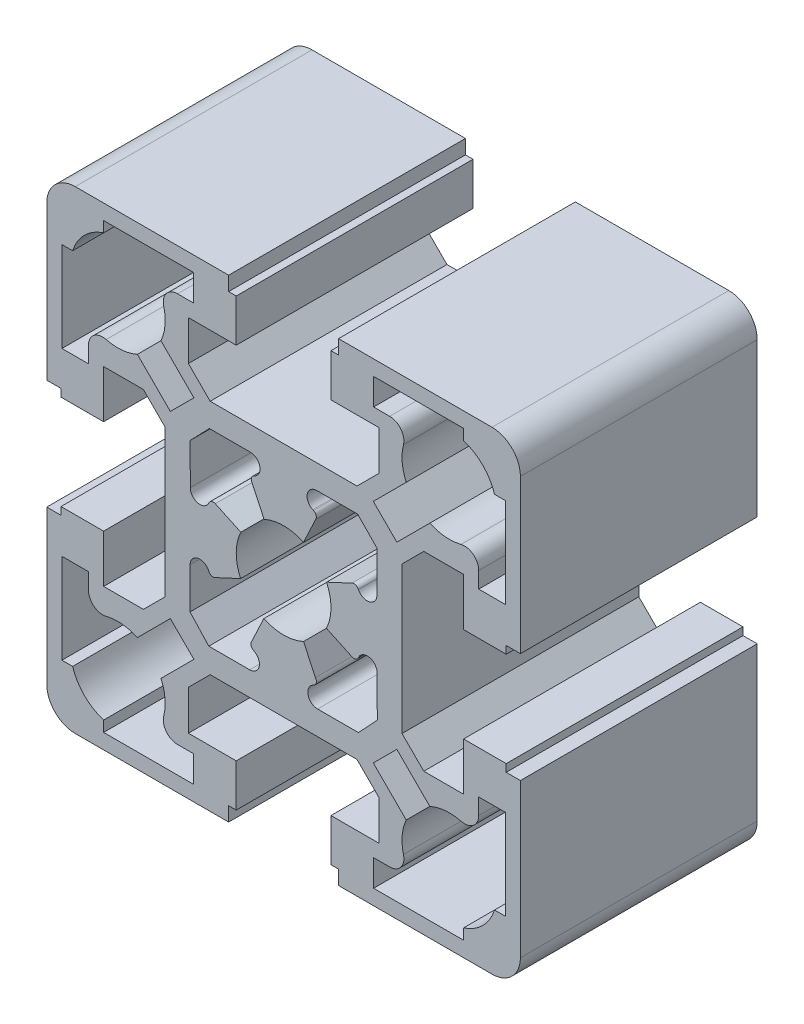
SolidWorks part; units mm, degrees
material "1060 Alloy"
ref_plane "Front" through (0, 0, 0) normal (0, 0, 1) x (1, 0, 0)
ref_plane "Top" through (0, 0, 0) normal (0, 1, 0) x (1, 0, 0)
ref_plane "Right" through (0, 0, 0) normal (1, 0, 0) x (0, 0, -1)
sketch "Sketch1" plane through (0, 0, 0) normal (0, 0, 1) x (1, 0, 0)
  line L164 (-19.1806, 22.5226) -> (-19.1806, 23.6529)
  line L165 (-19.1806, 23.6529) -> (-9.6806, 23.6529)
  line L166 (-9.6806, 23.6529) -> (-9.6806, 20.8529)
  line L167 (-9.6806, 20.8529) -> (-11.3805, 20.8529)
  line L168 (-13.1273, 15.6869) -> (-9.6488, 12.2083)
  line L169 (-9.6488, 12.2083) -> (-12.136, 9.7211)
  line L170 (-12.136, 9.7211) -> (-15.6145, 13.1996)
  line L171 (-20.7806, 11.4528) -> (-20.7806, 9.7529)
  line L172 (-20.7806, 9.7529) -> (-23.5806, 9.7529)
  line L173 (-23.5806, 9.7529) -> (-23.5806, 19.2529)
  line L174 (-23.5806, 19.2529) -> (-22.4503, 19.2529)
  line L175 (11.0192, 20.8529) -> (9.3194, 20.8529)
  line L176 (9.2875, 12.2083) -> (12.766, 15.6869)
  line L177 (11.7748, 9.7211) -> (9.2875, 12.2083)
  line L178 (15.2533, 13.1996) -> (11.7748, 9.7211)
  line L179 (20.4194, 9.7529) -> (20.4194, 11.4528)
  line L180 (23.2194, 9.7529) -> (20.4194, 9.7529)
  line L181 (23.2194, 19.2529) -> (23.2194, 9.7529)
  line L182 (22.0891, 19.2529) -> (23.2194, 19.2529)
  line L183 (18.8194, 23.6529) -> (18.8194, 22.5226)
  line L184 (9.3194, 23.6529) -> (18.8194, 23.6529)
  line L185 (9.3194, 20.8529) -> (9.3194, 23.6529)
  line L186 (18.8194, -23.1471) -> (9.3194, -23.1471)
  line L187 (18.8194, -22.0168) -> (18.8194, -23.1471)
  line L188 (23.2194, -18.7471) -> (22.0891, -18.7471)
  line L189 (23.2194, -9.2471) -> (23.2194, -18.7471)
  line L190 (20.4194, -9.2471) -> (23.2194, -9.2471)
  line L191 (20.4194, -10.9469) -> (20.4194, -9.2471)
  line L192 (11.7748, -9.2152) -> (15.2533, -12.6937)
  line L193 (9.2875, -11.7025) -> (11.7748, -9.2152)
  line L194 (12.766, -15.181) -> (9.2875, -11.7025)
  line L195 (9.3194, -20.3471) -> (11.0192, -20.3471)
  line L196 (9.3194, -23.1471) -> (9.3194, -20.3471)
  line L197 (-12.136, -9.2152) -> (-9.6488, -11.7025)
  line L198 (-9.6488, -11.7025) -> (-13.1273, -15.181)
  line L199 (-11.3805, -20.3471) -> (-9.6806, -20.3471)
  line L200 (-9.6806, -20.3471) -> (-9.6806, -23.1471)
  line L201 (-9.6806, -23.1471) -> (-19.1806, -23.1471)
  line L202 (5.6194, -24.7471) -> (21.8194, -24.7471)
  line L203 (24.8194, -21.7471) -> (24.8194, -5.5471)
  line L204 (24.8194, -5.5471) -> (23.3194, -5.5471)
  line L205 (23.3194, -5.5471) -> (23.3194, -4.7471)
  line L206 (23.3194, -4.7471) -> (18.8194, -4.7471)
  line L207 (18.8194, -4.7471) -> (18.8194, -9.7971)
  line L208 (18.8194, -9.7971) -> (14.6194, -9.7971)
  line L209 (14.6194, -9.7971) -> (12.3194, -7.4971)
  line L210 (12.3194, -7.4971) -> (12.3194, 8.0029)
  line L211 (12.3194, 8.0029) -> (14.6194, 10.3029)
  line L212 (14.6194, 10.3029) -> (18.8194, 10.3029)
  line L213 (18.8194, 10.3029) -> (18.8194, 5.2529)
  line L214 (18.8194, 5.2529) -> (23.3194, 5.2529)
  line L215 (23.3194, 5.2529) -> (23.3194, 6.0529)
  line L216 (23.3194, 6.0529) -> (24.8194, 6.0529)
  line L217 (24.8194, 6.0529) -> (24.8194, 22.2529)
  line L218 (21.8194, 25.2529) -> (5.6194, 25.2529)
  line L219 (5.6194, 25.2529) -> (5.6194, 23.7529)
  line L220 (5.6194, 23.7529) -> (4.8194, 23.7529)
  line L221 (4.8194, 23.7529) -> (4.8194, 19.2529)
  line L222 (4.8194, 19.2529) -> (9.8694, 19.2529)
  line L223 (9.8694, 19.2529) -> (9.8694, 15.0529)
  line L224 (9.8694, 15.0529) -> (7.5694, 12.7529)
  line L225 (7.5694, 12.7529) -> (-7.9306, 12.7529)
  line L226 (-7.9306, 12.7529) -> (-10.2306, 15.0529)
  line L227 (-10.2306, 15.0529) -> (-10.2306, 19.2529)
  line L228 (-10.2306, 19.2529) -> (-5.1806, 19.2529)
  line L229 (-5.1806, 19.2529) -> (-5.1806, 23.7529)
  line L230 (-5.1806, 23.7529) -> (-5.9806, 23.7529)
  line L231 (-5.9806, 23.7529) -> (-5.9806, 25.2529)
  line L232 (-5.9806, 25.2529) -> (-22.1806, 25.2529)
  line L233 (-25.1806, 22.2529) -> (-25.1806, 6.0529)
  line L234 (-25.1806, 6.0529) -> (-23.6806, 6.0529)
  line L235 (-23.6806, 6.0529) -> (-23.6806, 5.2529)
  line L236 (-23.6806, 5.2529) -> (-19.1806, 5.2529)
  line L237 (-19.1806, 5.2529) -> (-19.1806, 10.3029)
  line L238 (-19.1806, 10.3029) -> (-14.9806, 10.3029)
  line L239 (-14.9806, 10.3029) -> (-12.6806, 8.0029)
  line L240 (-12.6806, 8.0029) -> (-12.6806, -7.4971)
  line L241 (-12.6806, -7.4971) -> (-14.9806, -9.7971)
  line L242 (-14.9806, -9.7971) -> (-19.1806, -9.7971)
  line L243 (-19.1806, -9.7971) -> (-19.1806, -4.7471)
  line L244 (-19.1806, -4.7471) -> (-23.6806, -4.7471)
  line L245 (-23.6806, -4.7471) -> (-23.6806, -5.5471)
  line L246 (-23.6806, -5.5471) -> (-25.1806, -5.5471)
  line L247 (-25.1806, -5.5471) -> (-25.1806, -21.7471)
  line L248 (-22.1806, -24.7471) -> (-5.9806, -24.7471)
  line L249 (-5.9806, -24.7471) -> (-5.9806, -23.2471)
  line L250 (-5.9806, -23.2471) -> (-5.1806, -23.2471)
  line L251 (-5.1806, -23.2471) -> (-5.1806, -18.7471)
  line L252 (-5.1806, -18.7471) -> (-10.2306, -18.7471)
  line L253 (-10.2306, -18.7471) -> (-10.2306, -14.5471)
  line L254 (-10.2306, -14.5471) -> (-7.9306, -12.2471)
  line L255 (-7.9306, -12.2471) -> (7.5694, -12.2471)
  line L256 (7.5694, -12.2471) -> (9.8694, -14.5471)
  line L257 (9.8694, -14.5471) -> (9.8694, -18.7471)
  line L258 (9.8694, -18.7471) -> (4.8194, -18.7471)
  line L259 (4.8194, -18.7471) -> (4.8194, -23.2471)
  line L260 (4.8194, -23.2471) -> (5.6194, -23.2471)
  line L261 (5.6194, -23.2471) -> (5.6194, -24.7471)
  line L262 (-19.1806, -23.1471) -> (-19.1806, -22.0168)
  line L263 (-22.4503, -18.7471) -> (-23.5806, -18.7471)
  line L264 (-23.5806, -18.7471) -> (-23.5806, -9.2471)
  line L265 (-23.5806, -9.2471) -> (-20.7806, -9.2471)
  line L266 (-15.6145, -12.6937) -> (-12.136, -9.2152)
  line L267 (-20.7806, -9.2471) -> (-20.7806, -10.9469)
  line L268 (-4.6963, 2.3998) -> (-7.3892, 3.6555)
  line L269 (-10.031, 3.8032) -> (-10.0402, 8.1205)
  line L270 (-7.4089, -3.1075) -> (-4.716, -1.8518)
  line L271 (-10.0602, -7.5725) -> (-10.051, -3.2552)
  line L272 (-8.0783, -9.7128) -> (-10.0602, -7.5725)
  line L273 (-3.761, -9.7128) -> (-8.0783, -9.7128)
  line L274 (-2.2713, -4.289) -> (-3.5327, -6.9792)
  line L275 (3.1847, -6.9731) -> (1.9289, -4.2803)
  line L276 (7.7219, -9.7128) -> (3.4046, -9.7128)
  line L277 (9.7107, -7.5789) -> (7.7219, -9.7128)
  line L278 (9.6924, -3.2616) -> (9.7107, -7.5789)
  line L279 (4.3456, -1.8715) -> (7.0412, -3.1215)
  line L280 (7.0478, 3.6145) -> (4.3552, 2.3567)
  line L281 (9.679, 8.1307) -> (9.6698, 3.8134)
  line L282 (7.642, 10.2187) -> (9.679, 8.1307)
  line L283 (3.3247, 10.2187) -> (7.642, 10.2187)
  line L284 (1.9289, 4.7861) -> (3.1847, 7.479)
  line L285 (-3.5041, 7.4982) -> (-2.2426, 4.8079)
  line L286 (-8.0138, 10.2187) -> (-3.6965, 10.2187)
  line L287 (-10.0402, 8.1205) -> (-8.0138, 10.2187)
  line L288 (7.7051, -2.8782) -> (7.7264, -2.8323)
  line L289 (2.969, -7.7477) -> (3.0009, -7.7328)
  line L290 (-3.3533, -7.7428) -> (-3.325, -7.7561)
  line L291 (-8.0932, -2.8233) -> (-8.0734, -2.8657)
  line L292 (-8.0536, 3.4136) -> (-8.0733, 3.3714)
  line L293 (-3.2605, 8.2619) -> (-3.3081, 8.2396)
  line L294 (2.9834, 8.2164) -> (2.8924, 8.2586)
  arc A29 (-19.1806, 22.5226) -> (-22.4503, 19.2529) centre (-17.6806, 17.7529) ccw
  arc A30 (-11.3805, 20.8529) -> (-12.8343, 18.9837) centre (-11.3805, 19.3529) ccw
  arc A31 (-13.1273, 15.6869) -> (-12.8343, 18.9837) centre (-17.6806, 17.7529) ccw
  arc A32 (-18.9114, 12.9066) -> (-15.6145, 13.1996) centre (-17.6806, 17.7529) ccw
  arc A33 (-18.9114, 12.9066) -> (-20.7806, 11.4528) centre (-19.2806, 11.4528) ccw
  arc A34 (21.8194, -24.7471) -> (24.8194, -21.7471) centre (21.8194, -21.7471) ccw
  arc A35 (24.8194, 22.2529) -> (21.8194, 25.2529) centre (21.8194, 22.2529) ccw
  arc A36 (-22.1806, 25.2529) -> (-25.1806, 22.2529) centre (-22.1806, 22.2529) ccw
  arc A37 (-25.1806, -21.7471) -> (-22.1806, -24.7471) centre (-22.1806, -21.7471) ccw
  arc A38 (12.4731, 18.9837) -> (11.0192, 20.8529) centre (11.0192, 19.3529) ccw
  arc A39 (12.4731, 18.9837) -> (12.766, 15.6869) centre (17.3194, 17.7529) ccw
  arc A40 (15.2533, 13.1996) -> (18.5502, 12.9066) centre (17.3194, 17.7529) ccw
  arc A41 (20.4194, 11.4528) -> (18.5502, 12.9066) centre (18.9194, 11.4528) ccw
  arc A42 (22.0891, 19.2529) -> (18.8194, 22.5226) centre (17.3194, 17.7529) ccw
  arc A43 (18.8194, -22.0168) -> (22.0891, -18.7471) centre (17.3194, -17.2471) ccw
  arc A44 (18.5502, -12.4008) -> (20.4194, -10.9469) centre (18.9194, -10.9469) ccw
  arc A45 (18.5502, -12.4008) -> (15.2533, -12.6937) centre (17.3194, -17.2471) ccw
  arc A46 (12.766, -15.181) -> (12.4731, -18.4778) centre (17.3194, -17.2471) ccw
  arc A47 (11.0192, -20.3471) -> (12.4731, -18.4778) centre (11.0192, -18.8471) ccw
  arc A48 (-12.8343, -18.4778) -> (-13.1273, -15.181) centre (-17.6806, -17.2471) ccw
  arc A49 (-12.8343, -18.4778) -> (-11.3805, -20.3471) centre (-11.3805, -18.8471) ccw
  arc A50 (-22.4503, -18.7471) -> (-19.1806, -22.0168) centre (-17.6806, -17.2471) ccw
  arc A51 (-15.6145, -12.6937) -> (-18.9114, -12.4008) centre (-17.6806, -17.2471) ccw
  arc A52 (-20.7806, -10.9469) -> (-18.9114, -12.4008) centre (-19.2806, -10.9469) ccw
  arc A53 (-7.3892, 3.6555) -> (-8.0536, 3.4136) centre (-7.6005, 3.2023) ccw
  arc A54 (-10.031, 3.8032) -> (-8.0733, 3.3714) centre (-9.0041, 3.8054) ccw
  arc A55 (-4.6963, 2.3998) -> (-4.716, -1.8518) centre (-0.1806, 0.2529) ccw
  arc A56 (-8.0734, -2.8657) -> (-7.4089, -3.1075) centre (-7.6203, -2.6544) ccw
  arc A57 (-8.0932, -2.8233) -> (-10.051, -3.2552) centre (-9.024, -3.2573) ccw
  arc A58 (-3.761, -9.7128) -> (-3.325, -7.7561) centre (-3.761, -8.6859) ccw
  arc A59 (-3.5327, -6.9792) -> (-3.3533, -7.7428) centre (-3.1411, -7.2901) ccw
  arc A60 (-2.2713, -4.289) -> (1.9289, -4.2803) centre (-0.1806, 0.2529) ccw
  arc A61 (3.0009, -7.7328) -> (3.1847, -6.9731) centre (2.7896, -7.2796) ccw
  arc A62 (2.969, -7.7477) -> (3.4046, -9.7128) centre (3.4046, -8.682) ccw
  arc A63 (9.6924, -3.2616) -> (7.7264, -2.8323) centre (8.6616, -3.266) ccw
  arc A64 (7.0412, -3.1215) -> (7.7051, -2.8782) centre (7.2515, -2.6679) ccw
  arc A65 (4.3456, -1.8715) -> (4.3552, 2.3567) centre (-0.1806, 0.2529) ccw
  arc A66 (7.7149, 3.3636) -> (9.6698, 3.8134) centre (8.6401, 3.8156) ccw
  arc A67 (3.3247, 10.2187) -> (2.8924, 8.2586) centre (3.3247, 9.191) ccw
  arc A68 (3.1847, 7.479) -> (2.9834, 8.2164) centre (2.773, 7.7628) ccw
  arc A69 (1.9289, 4.7861) -> (-2.2426, 4.8079) centre (-0.1806, 0.2529) ccw
  arc A70 (-3.3081, 8.2396) -> (-3.5041, 7.4982) centre (-3.0959, 7.7869) ccw
  arc A71 (-3.2605, 8.2619) -> (-3.6965, 10.2187) centre (-3.6965, 9.1918) ccw
  arc A72 (7.0478, 3.6145) -> (7.7149, 3.3636) centre (7.2587, 3.163) cw
  point P3 (7.8482, -3.0656)
extrude "Boss-Extrude1" add sketch "Sketch1" along normal blind 25
